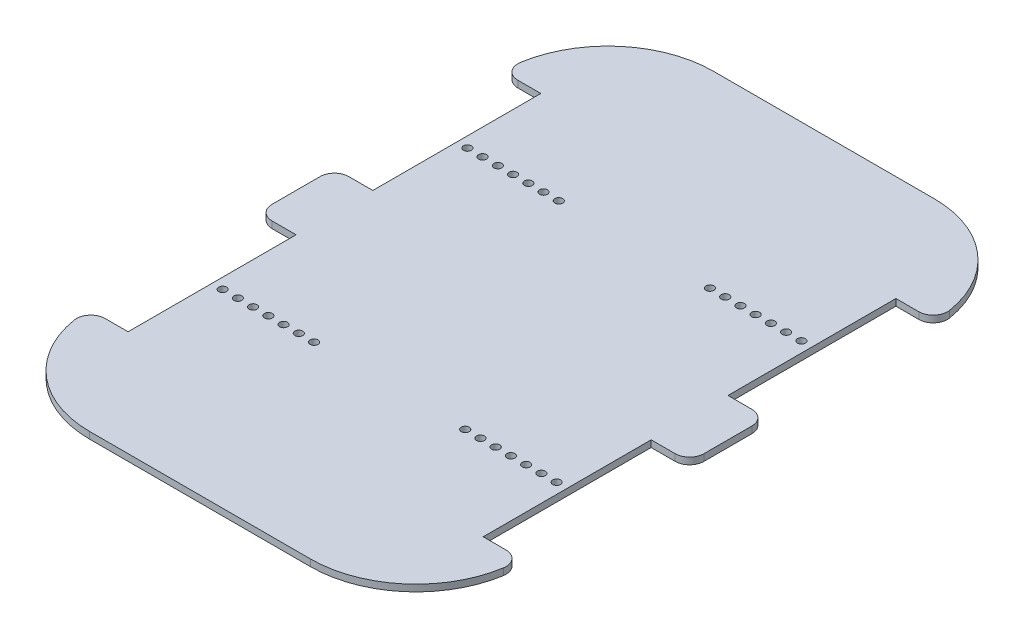
SolidWorks part; units mm, degrees
ref_plane "Ön Düzlem" through (0, 0, 0) normal (0, 0, 1) x (1, 0, 0)
ref_plane "Üst Düzlem" through (0, 0, 0) normal (0, 1, 0) x (1, 0, 0)
ref_plane "Sağ Düzlem" through (0, 0, 0) normal (1, 0, 0) x (0, 0, -1)
sketch "Sketch2" plane through (0, 0, 0) normal (0, 1, 0) x (1, 0, 0)
  line L0 (-74, -86) -> (-74, -51) construction
  line L1 (46, -130) -> (-46, -130)
  line L2 (90, -10) -> (90, 10)
  line L3 (46, 130) -> (-46, 130)
  line L4 (-90, -10) -> (-90, 10)
  line L5 (90, -130) -> (-90, 130) construction
  line L6 (90, 130) -> (-90, -130) construction
  line L7 (-83.5233, 86) -> (-74, 86)
  line L9 (-84, 16) -> (-74, 16)
  line L10 (-74, 86) -> (-74, 16)
  line L11 (-83.5233, -86) -> (-74, -86)
  line L13 (-84, -16) -> (-74, -16)
  line L14 (-74, -86) -> (-74, -16)
  line L15 (83.5233, 86) -> (74, 86)
  line L17 (84, 16) -> (74, 16)
  line L18 (74, 86) -> (74, 16)
  line L19 (83.5233, -86) -> (74, -86)
  line L21 (84, -16) -> (74, -16)
  line L22 (74, -86) -> (74, -16)
  line L23 (-74, 51) -> (74, 51) construction
  line L24 (-74, -51) -> (74, -51) construction
  arc A2 (-46, -130) -> (-89.4481, -92.9474) centre (-46, -86) cw
  arc A3 (-89.4481, 92.9474) -> (-46, 130) centre (-46, 86) cw
  arc A4 (89.4481, 92.9474) -> (46, 130) centre (46, 86) ccw
  arc A5 (89.4481, -92.9474) -> (46, -130) centre (46, -86) cw
  arc A6 (-84, 16) -> (-90, 10) centre (-84, 10) ccw
  arc A7 (-84, -16) -> (-90, -10) centre (-84, -10) cw
  arc A8 (90, 10) -> (84, 16) centre (84, 10) ccw
  arc A9 (90, -10) -> (84, -16) centre (84, -10) cw
  arc A10 (-89.4481, -92.9474) -> (-83.5233, -86) centre (-83.5233, -92) cw
  arc A11 (83.5233, -86) -> (89.4481, -92.9474) centre (83.5233, -92) cw
  arc A12 (-89.4481, 92.9474) -> (-83.5233, 86) centre (-83.5233, 92) ccw
  arc A13 (89.4481, 92.9474) -> (83.5233, 86) centre (83.5233, 92) cw
  point P0 (0, 0)
  point P34 (-90, -16)
  point P39 (90, -16)
  point P46 (-90, 86)
  point P49 (90, 86)
  dimension "D3" = 44
  dimension "D4" = 44
  dimension "D5" = 44
  dimension "D6" = 44
  dimension "D15" = 6
  dimension "D16" = 6
  dimension "D17" = 6
  dimension "D18" = 6
  dimension "D19" = 6
  dimension "D20" = 6
  dimension "D21" = 6
  dimension "D22" = 6
  dimension "D1" = 260
  dimension "D2" = 180
  dimension "D7" = 16
  dimension "D8" = 70
  dimension "D9" = 16
  dimension "D10" = 70
  dimension "D11" = 70
  dimension "D12" = 16
  dimension "D13" = 16
  dimension "D14" = 70
extrude "Boss-Extrude4" add sketch "Sketch2" along normal blind 2.8
sketch "Sketch5" plane through (0, 2.8, 0) normal (0, 1, 0) x (1, 0, 0)
  circle A0 centre (-69.6, -51) radius 1.65
  circle A1 centre (-63.25, -51) radius 1.65
  circle A2 centre (-56.9, -51) radius 1.65
  circle A3 centre (-50.55, -51) radius 1.65
  circle A4 centre (-44.2, -51) radius 1.65
  circle A5 centre (-37.85, -51) radius 1.65
  circle A6 centre (-31.5, -51) radius 1.65
  circle A7 centre (31.5, -51) radius 1.65
  circle A8 centre (37.85, -51) radius 1.65
  circle A9 centre (44.2, -51) radius 1.65
  circle A10 centre (50.55, -51) radius 1.65
  circle A11 centre (56.9, -51) radius 1.65
  circle A12 centre (63.25, -51) radius 1.65
  circle A13 centre (69.6, -51) radius 1.65
  circle A14 centre (69.6, 51) radius 1.65
  circle A15 centre (63.25, 51) radius 1.65
  circle A16 centre (56.9, 51) radius 1.65
  circle A17 centre (50.55, 51) radius 1.65
  circle A18 centre (44.2, 51) radius 1.65
  circle A19 centre (37.85, 51) radius 1.65
  circle A20 centre (31.5, 51) radius 1.65
  circle A21 centre (-31.5, 51) radius 1.65
  circle A22 centre (-37.85, 51) radius 1.65
  circle A23 centre (-44.2, 51) radius 1.65
  circle A24 centre (-50.55, 51) radius 1.65
  circle A25 centre (-56.9, 51) radius 1.65
  circle A26 centre (-63.25, 51) radius 1.65
  circle A27 centre (-69.6, 51) radius 1.65
extrude "Cut-Extrude1" cut sketch "Sketch5" against normal through all
